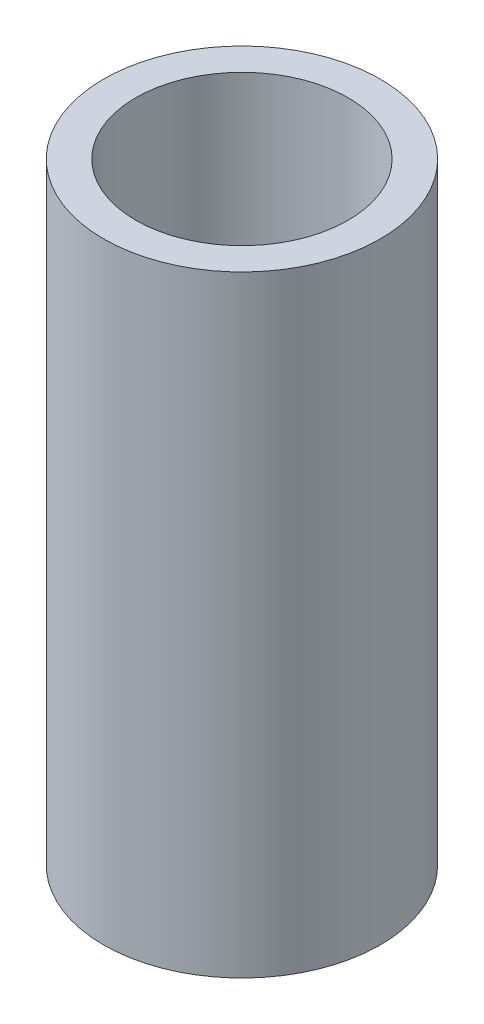
SolidWorks part; units mm, degrees
ref_plane "Front Plane" through (0, 0, 0) normal (0, 0, 1) x (1, 0, 0)
ref_plane "Top Plane" through (0, 0, 0) normal (0, 1, 0) x (1, 0, 0)
ref_plane "Right Plane" through (0, 0, 0) normal (1, 0, 0) x (0, 0, -1)
sketch "Sketch1" plane through (0, 0, 0) normal (0, 1, 0) x (1, 0, 0)
  circle A0 centre (0, 0) radius 1.65
  circle A1 centre (0, 0) radius 2.15
  dimension "D1" = 3.3
  dimension "D2" = 4.3
extrude "Boss-Extrude1" add sketch "Sketch1" along normal blind 9.5
